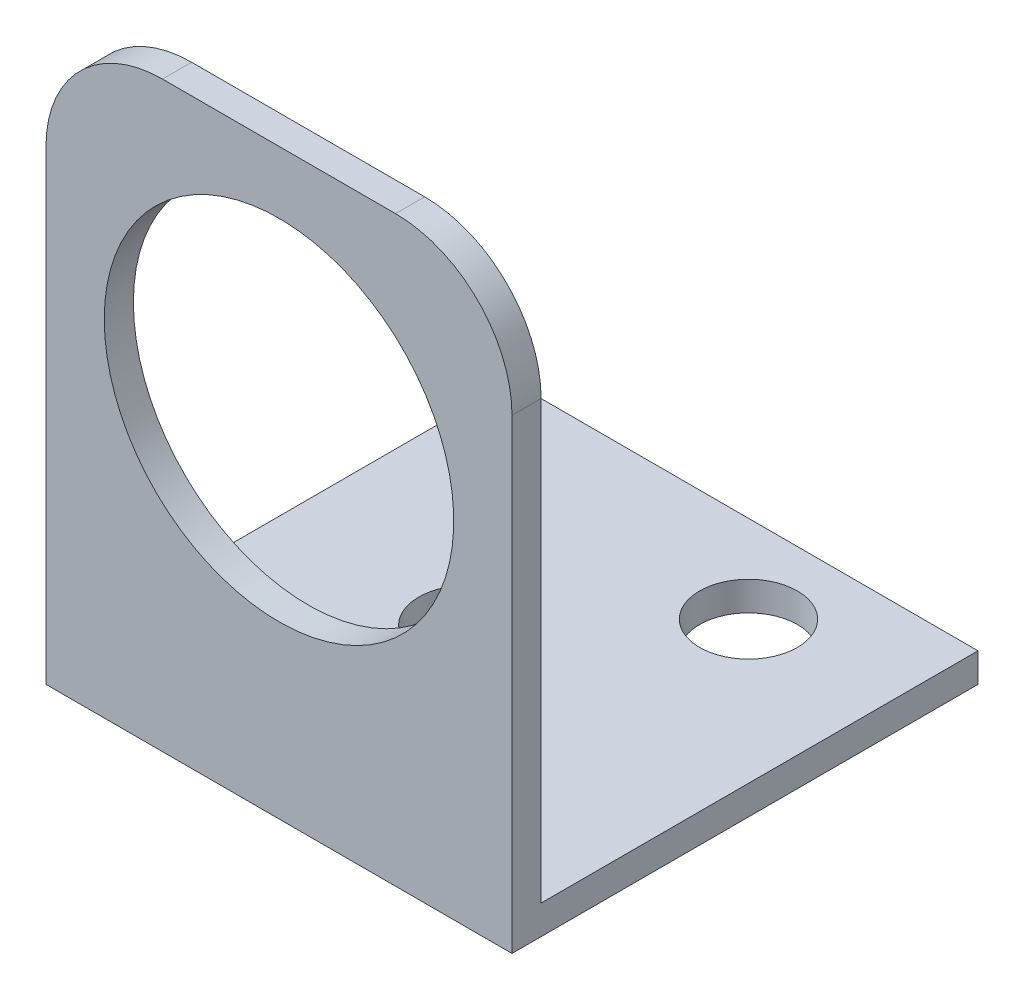
SolidWorks part; units mm, degrees
material "6061-T6 (SS)"
ref_plane "Front" through (0, 0, 0) normal (0, 0, 1) x (1, 0, 0)
ref_plane "Top" through (0, 0, 0) normal (0, 1, 0) x (1, 0, 0)
ref_plane "Right" through (0, 0, 0) normal (1, 0, 0) x (0, 0, -1)
sketch "Sketch1" plane through (0, 0, 0) normal (1, 0, 0) x (0, 0, -1)
  line L0 (1.5875, 1.5875) -> (25.4, 1.5875)
  line L1 (0, 0) -> (25.4, 0)
  line L2 (0, 0) -> (0, 31.75)
  line L5 (1.5875, 1.5875) -> (1.5875, 31.75)
  line L6 (25.4, 0) -> (25.4, 1.5875)
  line L7 (0, 31.75) -> (1.5875, 31.75)
  dimension "D1" = 31.75
  dimension "D2" = 25.4
  dimension "D3" = 1.5875
extrude "Boss-Extrude1" add sketch "Sketch1" along normal blind 25.4
sketch "Sketch2" plane through (0, 0, -1.5875) normal (0, 0, -1) x (-1, 0, 0)
  circle A0 centre (-12.7, 18.8307) radius 9.525 construction
  circle A1 centre (-12.7, 18.8307) radius 9.525
extrude "Cut-Extrude1" cut sketch "Sketch2" against normal up to next
fillet "Fillet1" radius 6.35 2 edges at (25.4, 31.75, -0.7937) (0, 31.75, -0.7937)
sketch "Sketch3" plane through (0, 0, 0) normal (0, -1, 0) x (1, 0, 0)
  line L1 (17.653, -20.6375) -> (17.653, -25.4) construction
  line L2 (25.4, -25.4) -> (0, -25.4) construction
  line L4 (10.287, -12.7) -> (10.287, -25.4) construction
  line L5 (7.62, 4.3539) -> (7.62, -55.9711) construction
  line L6 (20.32, 4.3539) -> (20.32, -55.9711) construction
  circle A0 centre (17.653, -20.6375) radius 2.667
  circle A1 centre (10.287, -12.7) radius 2.667
  dimension "D1" = 5.334
  dimension "D3" = 12.7
  dimension "D2" = 4.7625
extrude "Cut-Extrude2" cut sketch "Sketch3" against normal up to next
